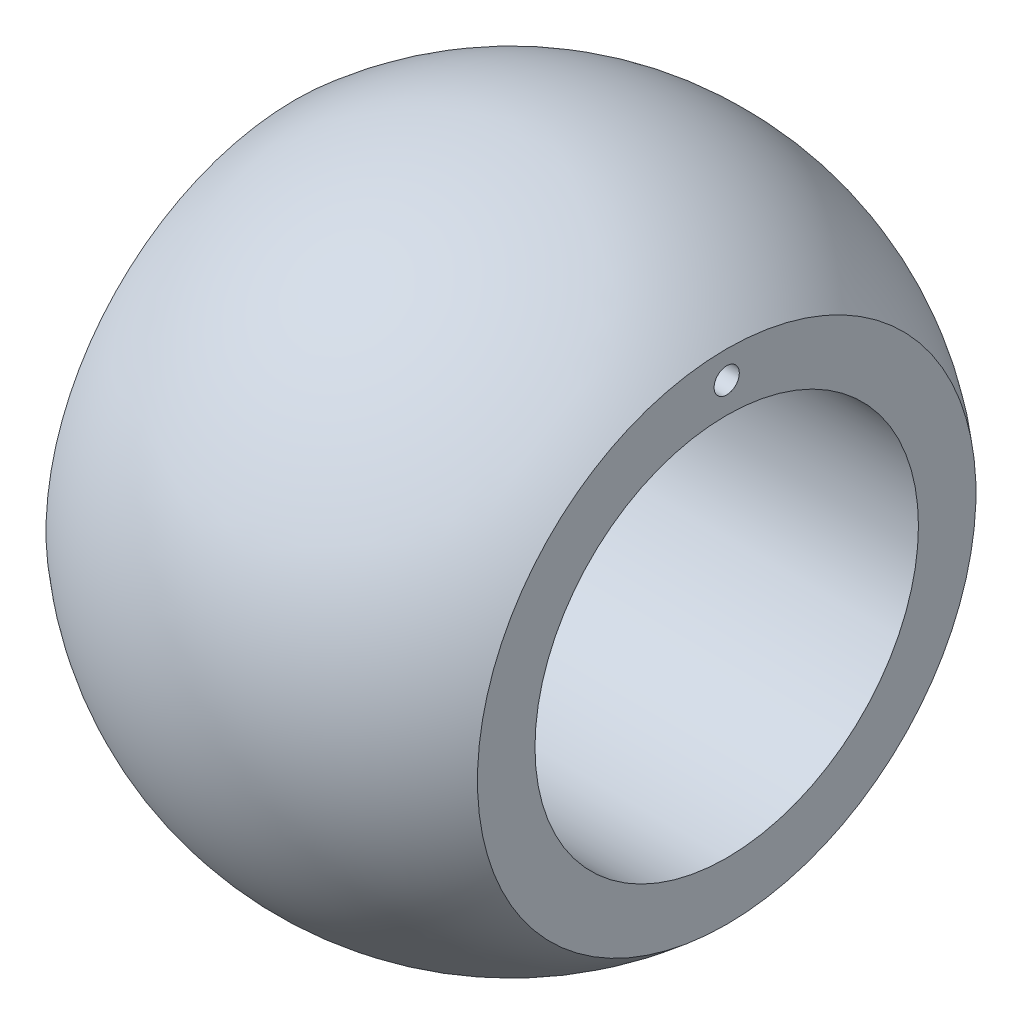
SolidWorks part; units mm, degrees
material "Alloy Steel"
ref_plane "Front Plane" through (0, 0, 0) normal (0, 0, 1) x (1, 0, 0)
ref_plane "Top Plane" through (0, 0, 0) normal (0, 1, 0) x (1, 0, 0)
ref_plane "Right Plane" through (0, 0, 0) normal (1, 0, 0) x (0, 0, -1)
sketch "Sketch1" plane through (0, 0, 0) normal (0, 0, 1) x (1, 0, 0)
  line L0 (-6.8768, 0) -> (6.8768, 0) construction
  line L1 (0, -29.3047) -> (0, -50029.3047) construction
  line L2 (-4.5, 4) -> (-4.5, 5.2)
  line L3 (4.5, 5.2) -> (4.5, 4)
  line L4 (4.5, 4) -> (-4.5, 4)
  arc A0 (-4.5, 5.2) -> (4.5, 5.2) centre (0, 0) cw
  circle A1 centre (0, 0) radius 6.8768 construction
  point P7 (0, 4)
  dimension "D1" = 9
  dimension "D2" = 10.4
  dimension "D3" = 8
revolve "Revolve1" add sketch "Sketch1" angle 360 about L0
sketch "Sketch2" plane through (4.5, 0, 0) normal (1, 0, 0) x (0, 0, -1)
  line L0 (0, 4.63) -> (0, 0) construction
  circle A0 centre (0, 4.63) radius 0.263
  dimension "D1" = 0.526
  dimension "D2" = 4.63
extrude "Cut-Extrude1" cut sketch "Sketch2" against normal through all both and the other way through all
